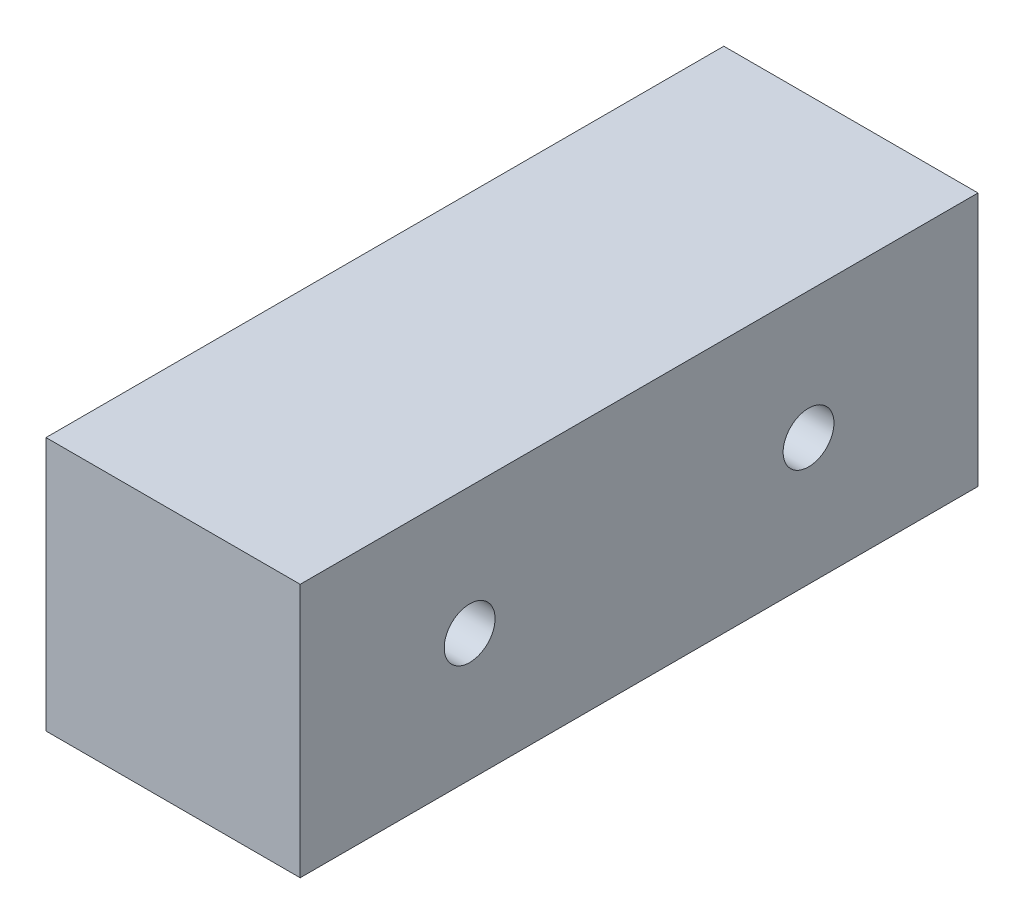
SolidWorks part; units mm, degrees
ref_plane "Front Plane" through (0, 0, 0) normal (0, 0, 1) x (1, 0, 0)
ref_plane "Top Plane" through (0, 0, 0) normal (0, 1, 0) x (1, 0, 0)
ref_plane "Right Plane" through (0, 0, 0) normal (1, 0, 0) x (0, 0, -1)
sketch "Sketch1" plane through (0, 0, 0) normal (0, 1, 0) x (1, 0, 0)
  line L1 (0, 0) -> (150, 0)
  line L2 (0, 0) -> (0, 400)
  line L3 (0, 400) -> (150, 400)
  line L4 (150, 0) -> (150, 400)
  dimension "D1" = 400
  dimension "D2" = 150
extrude "Boss-Extrude1" add sketch "Sketch1" along normal blind 150
sketch "Sketch2" plane through (150, 0, 0) normal (1, 0, 0) x (0, 0, -1)
  line L0 (400, 150) -> (400, 0) construction
  line L1 (0, 0) -> (400, 0) construction
  line L2 (0, 150) -> (0, 0) construction
  circle A0 centre (300, 75) radius 15
  circle A1 centre (100, 75) radius 15
  dimension "D1" = 30
  dimension "D2" = 30
  dimension "D3" = 100
  dimension "D4" = 75
  dimension "D5" = 100
  dimension "D6" = 75
extrude "Cut-Extrude1" cut sketch "Sketch2" against normal through all
